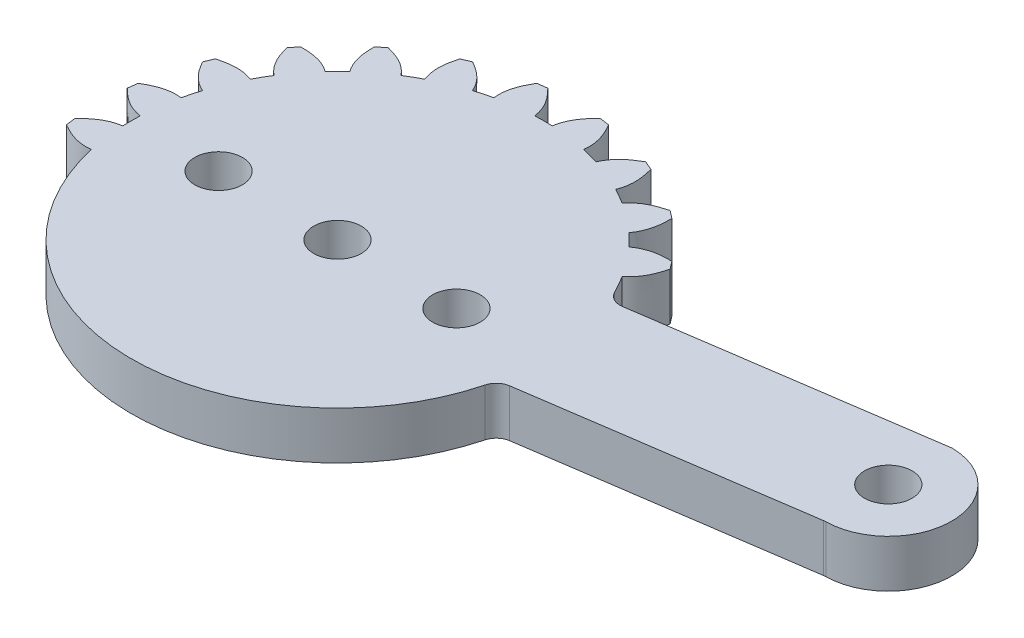
SolidWorks part; units mm, degrees
ref_plane "Front Plane" through (0, 0, 0) normal (0, 0, 1) x (1, 0, 0)
ref_plane "Top Plane" through (0, 0, 0) normal (0, 1, 0) x (1, 0, 0)
ref_plane "Right Plane" through (0, 0, 0) normal (1, 0, 0) x (0, 0, -1)
sketch "Sketch1" plane through (0, 0, 0) normal (0, 1, 0) x (1, 0, 0)
  line L0 (12.6327, 5.3405) -> (30.6525, 7.9886)
  line L1 (0, 0) -> (11.9003, 9.1314) construction
  line L2 (0, 0) -> (19.2179, 25.0452) construction
  line L3 (0, 0) -> (9.1924, 9.1924) construction
  line L5 (30.6617, -0.01) -> (13.4007, -2.5466)
  circle A2 centre (0, 0) radius 1.5
  circle A3 centre (7.5, 0) radius 1.5
  circle A4 centre (-7.5, 0) radius 1.5
  arc A5 (-12.4035, -3.8928) -> (12.5785, -3.2834) centre (0, 0) ccw
  circle A6 centre (30.73, 4) radius 1.5
  arc A8 (11.5954, 5.8777) -> (10.9732, 6.9706) centre (0, 0) ccw
  arc A9 (30.7917, 0.0005) -> (30.8205, 7.999) centre (30.73, 4) ccw
  arc A10 (30.6617, -0.01) -> (30.7917, 0.0005) centre (30.8071, -0.9994) cw
  arc A11 (30.6525, 7.9886) -> (30.8205, 7.999) centre (30.7979, 6.9992) cw
  arc A12 (12.6327, 5.3405) -> (11.5954, 5.8777) centre (12.4873, 6.3299) cw
  arc A13 (12.5785, -3.2834) -> (13.4007, -2.5466) centre (13.5461, -3.536) cw
  spline S0 degree 3 poles (9.5731, 8.7952) (10.2501, 9.2991) (10.982, 9.3793) (11.7091, 9.3754) knots 0 0 0 0 0.58557 0.58557 0.58557 0.58557
  spline S1 degree 2 poles (11.7091, 9.3754) (11.9028, 9.1334) (12.0865, 8.8835) knots 0 0 0 1 1 1
  spline S2 degree 3 poles (10.9732, 6.9706) (11.6352, 7.494) (11.9021, 8.1802) (12.0865, 8.8835) knots 0 0 0 0 0.58557 0.58557 0.58557 0.58557
  spline S4 degree 3 poles (8.7952, 9.5731) (9.2991, 10.2501) (9.3793, 10.982) (9.3754, 11.7091) knots 0 0 0 0 0.58557 0.58557 0.58557 0.58557
  spline S5 degree 2 poles (8.8835, 12.0865) (9.1334, 11.9028) (9.3754, 11.7091) knots 0 0 0 1 1 1
  spline S6 degree 3 poles (6.9706, 10.9732) (7.494, 11.6352) (8.1802, 11.9021) (8.8835, 12.0865) knots 0 0 0 0 0.58557 0.58557 0.58557 0.58557
  spline S7 degree 3 poles (6.0178, 11.5233) (6.3294, 12.3076) (6.2174, 13.0353) (6.0254, 13.7366) knots 0 0 0 0 0.58557 0.58557 0.58557 0.58557
  spline S8 degree 2 poles (5.4526, 13.9739) (5.7415, 13.8612) (6.0254, 13.7366) knots 0 0 0 1 1 1
  spline S9 degree 3 poles (3.893, 12.4034) (4.2273, 13.1783) (4.821, 13.6137) (5.4526, 13.9739) knots 0 0 0 0 0.58557 0.58557 0.58557 0.58557
  spline S10 degree 3 poles (2.8303, 12.6882) (2.9283, 13.5264) (2.6318, 14.2003) (2.2648, 14.828) knots 0 0 0 0 0.58557 0.58557 0.58557 0.58557
  spline S11 degree 2 poles (1.6501, 14.909) (1.9583, 14.8748) (2.2648, 14.828) knots 0 0 0 1 1 1
  spline S12 degree 3 poles (0.5501, 12.9884) (0.6724, 13.8234) (1.1332, 14.3976) (1.6501, 14.909) knots 0 0 0 0 0.58557 0.58557 0.58557 0.58557
  spline S13 degree 3 poles (-0.5501, 12.9884) (-0.6724, 13.8234) (-1.1332, 14.3976) (-1.6501, 14.909) knots 0 0 0 0 0.58557 0.58557 0.58557 0.58557
  spline S14 degree 2 poles (-2.2648, 14.828) (-1.9583, 14.8748) (-1.6501, 14.909) knots 0 0 0 1 1 1
  spline S15 degree 3 poles (-2.8303, 12.6882) (-2.9283, 13.5264) (-2.6318, 14.2003) (-2.2648, 14.828) knots 0 0 0 0 0.58557 0.58557 0.58557 0.58557
  spline S16 degree 3 poles (-3.893, 12.4034) (-4.2273, 13.1783) (-4.821, 13.6137) (-5.4526, 13.9739) knots 0 0 0 0 0.58557 0.58557 0.58557 0.58557
  spline S17 degree 2 poles (-6.0254, 13.7366) (-5.7415, 13.8612) (-5.4526, 13.9739) knots 0 0 0 1 1 1
  spline S18 degree 3 poles (-6.0178, 11.5233) (-6.3294, 12.3076) (-6.2174, 13.0353) (-6.0254, 13.7366) knots 0 0 0 0 0.58557 0.58557 0.58557 0.58557
  spline S19 degree 3 poles (-6.9706, 10.9732) (-7.494, 11.6352) (-8.1802, 11.9021) (-8.8835, 12.0865) knots 0 0 0 0 0.58557 0.58557 0.58557 0.58557
  spline S20 degree 2 poles (-9.3754, 11.7091) (-9.1334, 11.9028) (-8.8835, 12.0865) knots 0 0 0 1 1 1
  spline S21 degree 3 poles (-8.7952, 9.5731) (-9.2991, 10.2501) (-9.3793, 10.982) (-9.3754, 11.7091) knots 0 0 0 0 0.58557 0.58557 0.58557 0.58557
  spline S22 degree 3 poles (-9.5731, 8.7952) (-10.2501, 9.2991) (-10.982, 9.3793) (-11.7091, 9.3754) knots 0 0 0 0 0.58557 0.58557 0.58557 0.58557
  spline S23 degree 2 poles (-12.0865, 8.8835) (-11.9028, 9.1334) (-11.7091, 9.3754) knots 0 0 0 1 1 1
  spline S24 degree 3 poles (-10.9732, 6.9706) (-11.6352, 7.494) (-11.9021, 8.1802) (-12.0865, 8.8835) knots 0 0 0 0 0.58557 0.58557 0.58557 0.58557
  spline S25 degree 3 poles (-11.5233, 6.0178) (-12.3076, 6.3294) (-13.0353, 6.2174) (-13.7366, 6.0254) knots 0 0 0 0 0.58557 0.58557 0.58557 0.58557
  spline S26 degree 2 poles (-13.9739, 5.4526) (-13.8612, 5.7415) (-13.7366, 6.0254) knots 0 0 0 1 1 1
  spline S27 degree 3 poles (-12.4034, 3.893) (-13.1783, 4.2273) (-13.6137, 4.821) (-13.9739, 5.4526) knots 0 0 0 0 0.58557 0.58557 0.58557 0.58557
  spline S28 degree 3 poles (-12.6882, 2.8303) (-13.5264, 2.9283) (-14.2003, 2.6318) (-14.828, 2.2648) knots 0 0 0 0 0.58557 0.58557 0.58557 0.58557
  spline S29 degree 2 poles (-14.909, 1.6501) (-14.8748, 1.9583) (-14.828, 2.2648) knots 0 0 0 1 1 1
  spline S30 degree 3 poles (-12.9884, 0.5501) (-13.8234, 0.6724) (-14.3976, 1.1332) (-14.909, 1.6501) knots 0 0 0 0 0.58557 0.58557 0.58557 0.58557
  spline S31 degree 3 poles (-12.9884, -0.5501) (-13.8234, -0.6724) (-14.3976, -1.1332) (-14.909, -1.6501) knots 0 0 0 0 0.58557 0.58557 0.58557 0.58557
  spline S32 degree 2 poles (-14.828, -2.2648) (-14.8748, -1.9583) (-14.909, -1.6501) knots 0 0 0 1 1 1
  spline S33 degree 3 poles (-12.6882, -2.8303) (-13.5264, -2.9283) (-14.2003, -2.6318) (-14.828, -2.2648) knots 0 0 0 0 0.58557 0.58557 0.58557 0.58557
  spline S34 degree 2 poles (-12.4035, -3.8928) (-12.5684, -3.3677) (-12.6882, -2.8303) knots 0 0 0 0.029411 0.029411 0.029411
  spline S35 degree 3 poles (-12.9884, -0.5501) (-13.0039, -0.1835) (-13.0039, 0.1835) (-12.9884, 0.5501) knots 0.090903 0.090903 0.090903 0.090903 0.120321 0.120321 0.120321 0.120321
  spline S36 degree 3 poles (-12.6882, 2.8303) (-12.6083, 3.1884) (-12.5134, 3.5429) (-12.4034, 3.893) knots 0.181813 0.181813 0.181813 0.181813 0.211231 0.211231 0.211231 0.211231
  spline S37 degree 3 poles (-11.5233, 6.0178) (-11.3535, 6.3431) (-11.17, 6.6609) (-10.9732, 6.9706) knots 0.272722 0.272722 0.272722 0.272722 0.302141 0.302141 0.302141 0.302141
  spline S38 degree 3 poles (-9.5731, 8.7952) (-9.3249, 9.0654) (-9.0654, 9.3249) (-8.7952, 9.5731) knots 0.363632 0.363632 0.363632 0.363632 0.39305 0.39305 0.39305 0.39305
  spline S39 degree 3 poles (-6.9706, 10.9732) (-6.6609, 11.17) (-6.3431, 11.3535) (-6.0178, 11.5233) knots 0.454542 0.454542 0.454542 0.454542 0.48396 0.48396 0.48396 0.48396
  spline S40 degree 3 poles (-3.893, 12.4034) (-3.5429, 12.5134) (-3.1884, 12.6083) (-2.8303, 12.6882) knots 0.545452 0.545452 0.545452 0.545452 0.57487 0.57487 0.57487 0.57487
  spline S41 degree 3 poles (-0.5501, 12.9884) (-0.1835, 13.0039) (0.1835, 13.0039) (0.5501, 12.9884) knots 0.636361 0.636361 0.636361 0.636361 0.665779 0.665779 0.665779 0.665779
  spline S42 degree 3 poles (2.8303, 12.6882) (3.1884, 12.6083) (3.5429, 12.5134) (3.893, 12.4034) knots 0.727271 0.727271 0.727271 0.727271 0.756689 0.756689 0.756689 0.756689
  spline S43 degree 3 poles (6.0178, 11.5233) (6.3431, 11.3535) (6.6609, 11.17) (6.9706, 10.9732) knots 0.818181 0.818181 0.818181 0.818181 0.847599 0.847599 0.847599 0.847599
  spline S44 degree 3 poles (8.7952, 9.5731) (9.0655, 9.3249) (9.325, 9.0653) (9.5731, 8.7952) knots 0.90909 0.90909 0.90909 0.90909 0.938508 0.938508 0.938508 0.938508
  point P32 (30.73, 0)
  point P74 (0, 0)
  point P77 (30.73, 8)
  point P98 (0, 0)
  dimension "D1" = 3
  dimension "D4" = 23.23
  dimension "D5" = 8
  dimension "D15" = 3
  dimension "D7" = 1
  dimension "D2" = 7.5
  dimension "D3" = 15
  dimension "D6" = 4
extrude "Boss-Extrude1" add sketch "Sketch1" along normal blind 3
